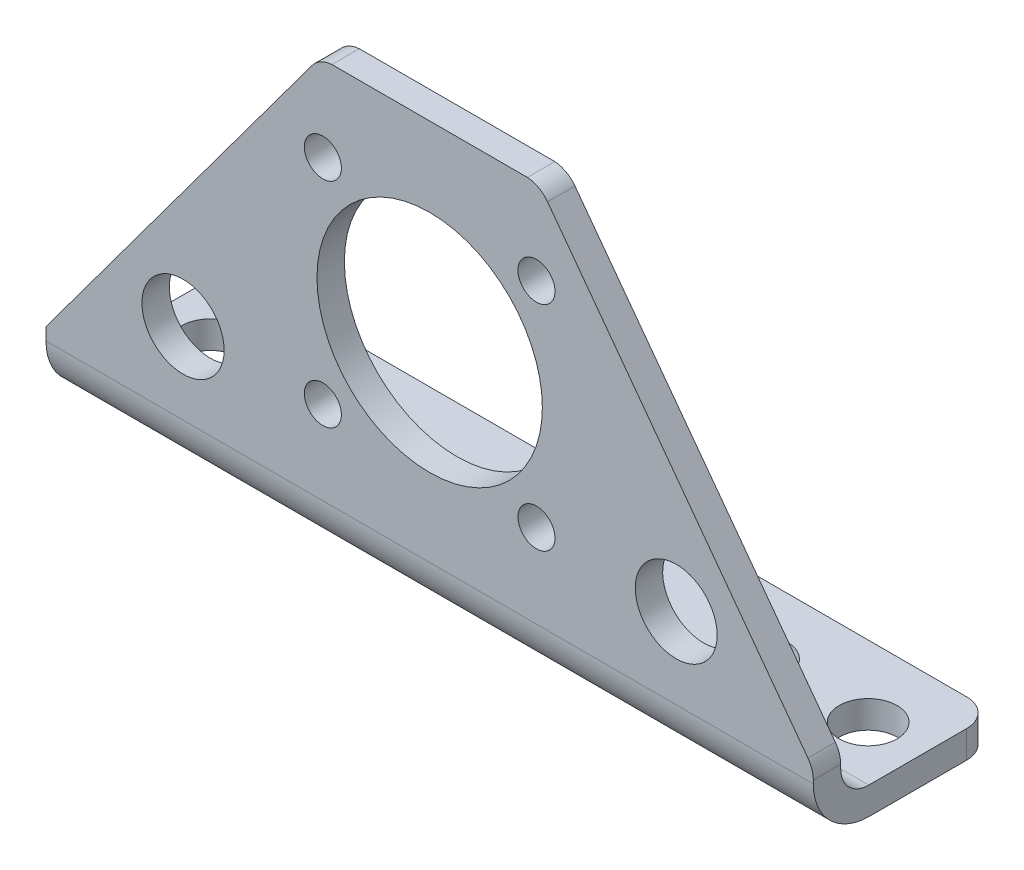
SolidWorks part; units mm, degrees
ref_plane "Front Plane" through (0, 0, 0) normal (0, 0, 1) x (1, 0, 0)
ref_plane "Top Plane" through (0, 0, 0) normal (0, 1, 0) x (1, 0, 0)
ref_plane "Right Plane" through (0, 0, 0) normal (1, 0, 0) x (0, 0, -1)
sketch "Sketch1" plane through (0, 0, 0) normal (-1, 0, 0) x (0, 0, 1)
  line L0 (-20.955, -28.575) -> (-6.5, -28.575)
  line L1 (0, -22.075) -> (0, 22.225)
  line L2 (0, 22.225) -> (-3.175, 22.225)
  line L3 (-3.175, 22.225) -> (-3.175, -22.15)
  line L5 (-20.955, -25.4) -> (-6.425, -25.4)
  line L7 (-20.955, -25.4) -> (-20.955, -28.575)
  arc A0 (-6.425, -25.4) -> (-3.175, -22.15) centre (-6.425, -22.15) ccw
  arc A1 (0, -22.075) -> (-6.5, -28.575) centre (-6.5, -22.075) cw
  dimension "D1" = 3.25
  dimension "D2" = 6.5
extrude "Boss-Extrude1" add sketch "Sketch1" against normal mid plane 88.9 separate body
sketch "Sketch2" plane through (0, -28.575, 0) normal (0, -1, 0) x (1, 0, 0)
  line L1 (-41.2803, -20.9487) -> (41.275, -20.9487)
  line L2 (-44.4553, -17.7737) -> (-44.4553, 4.5353)
  line L3 (-44.4553, 4.5353) -> (44.45, 4.5353)
  line L4 (44.45, -17.7737) -> (44.45, 4.5353)
  circle A0 centre (-38.1, -12.7) radius 3.3528
  circle A1 centre (-25.4, -12.7) radius 3.3528
  circle A3 centre (0, -12.7) radius 6.35
  circle A4 centre (25.4, -12.7) radius 3.3528
  circle A5 centre (38.1, -12.7) radius 3.3528
  arc A6 (-41.2803, -20.9487) -> (-44.4553, -17.7737) centre (-41.2803, -17.7737) cw
  arc A7 (44.45, -17.7737) -> (41.275, -20.9487) centre (41.275, -17.7737) cw
  dimension "D1" = 3.175
  dimension "D2" = 3.175
sketch "Sketch3" plane through (0, 0, 0) normal (0, 0, 1) x (1, 0, 0)
  line L0 (-13.6539, 20.9472) -> (-44.4508, -20.6317)
  line L1 (-11.1025, 22.2325) -> (11.1028, 22.2325)
  line L2 (-44.4508, -20.6317) -> (-44.4508, -28.575)
  line L3 (-44.4508, -28.575) -> (44.45, -28.575)
  line L4 (44.45, -21.6744) -> (44.45, -28.575)
  line L5 (13.654, 20.9473) -> (43.8263, -19.7845)
  circle A0 centre (-12.3748, 12.3748) radius 2.1463
  circle A1 centre (12.3748, 12.3748) radius 2.1463
  circle A2 centre (0, 0) radius 13.0556
  circle A3 centre (-28.575, -12.7) radius 4.7625
  circle A4 centre (-12.3748, -12.3748) radius 2.1463
  circle A5 centre (12.3748, -12.3748) radius 2.1463
  circle A6 centre (28.5648, -12.7158) radius 4.7437
  arc A7 (-11.1025, 22.2325) -> (-13.6539, 20.9472) centre (-11.1025, 19.0575) ccw
  arc A8 (13.654, 20.9473) -> (11.1028, 22.2325) centre (11.1028, 19.0575) ccw
  arc A9 (44.45, -21.6744) -> (43.8263, -19.7845) centre (41.275, -21.6744) ccw
  dimension "D1" = 3.175
  dimension "D2" = 3.175
  dimension "D3" = 3.175
extrude "Cut-Extrude3" cut sketch "Sketch2" against normal through all flip side to cut
extrude "Cut-Extrude4" cut sketch "Sketch3" against normal through all flip side to cut
